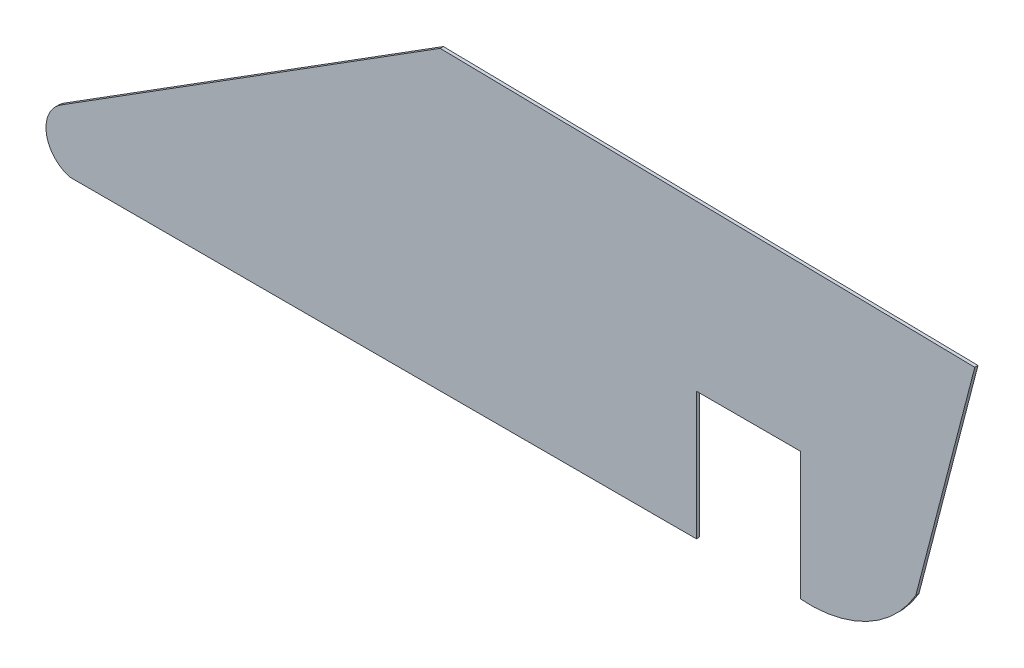
SolidWorks part; units mm, degrees
ref_plane "Alzado" through (0, 0, 0) normal (0, 0, 1) x (1, 0, 0)
ref_plane "Planta" through (0, 0, 0) normal (0, 1, 0) x (1, 0, 0)
ref_plane "Vista lateral" through (0, 0, 0) normal (1, 0, 0) x (0, 0, -1)
sketch "Model" plane through (0, 0, 0) normal (0, 0, 1) x (1, 0, 0)
  line L0 (16.5107, 0.4521) -> (33.229, 0.1739)
  line L1 (16.5107, 0.4521) -> (4.6496, -7.0114)
  line L2 (24.5222, -8.8268) -> (9.272, -8.8268)
  line L3 (4.9351, -8.8268) -> (24.5222, -8.8268)
  line L4 (31.3831, -6.9279) -> (33.229, 0.1739)
  line L5 (27.7722, -4.8268) -> (27.7722, -8.8268)
  line L6 (24.5222, -4.8268) -> (27.7722, -4.8268)
  line L7 (24.5222, -8.8268) -> (24.5222, -4.8268)
  arc A0 (4.6496, -7.0114) -> (4.9351, -8.8268) centre (5.1821, -7.8578) ccw
  arc A1 (27.7722, -8.8268) -> (31.3831, -6.9279) centre (28.0731, -5.0162) ccw
  point P12 (0, 0)
extrude "Saliente-Extruir1" add sketch "Model" along normal blind 0.1 contours L5 A1 L4 L0 L1 A0 L3 L2 L7 L6
